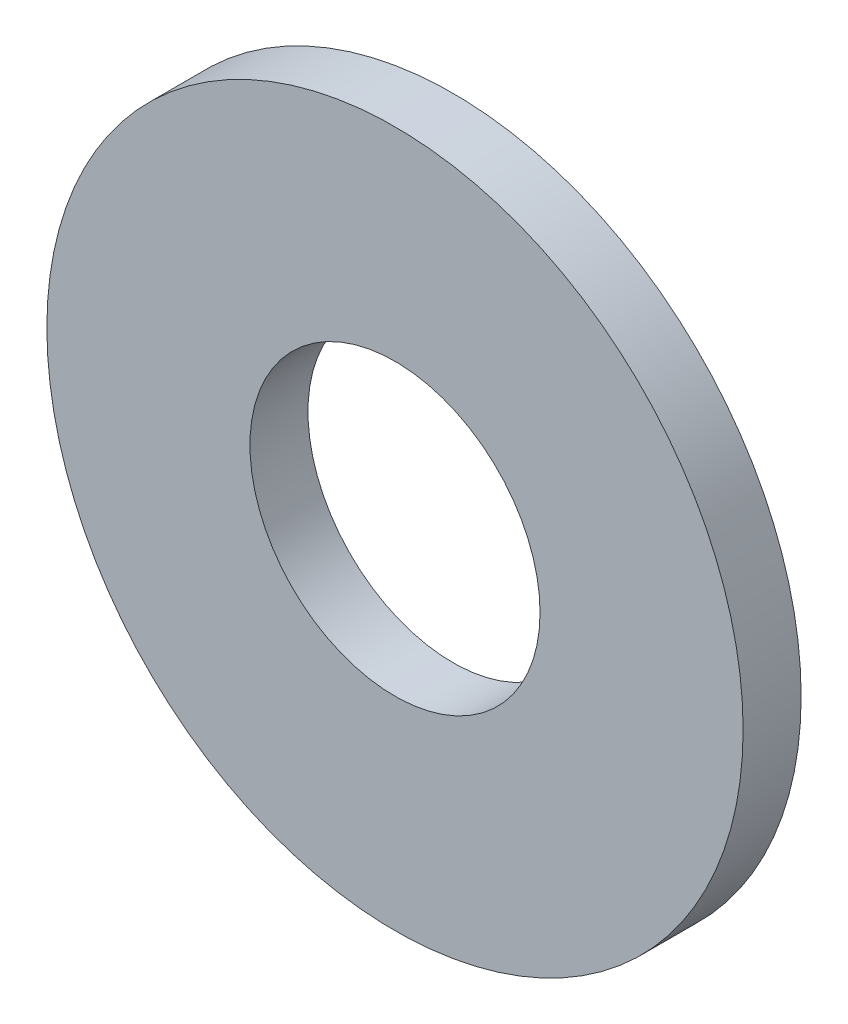
SolidWorks part; units mm, degrees
material "Plain Carbon Steel"
ref_plane "Front" through (0, 0, 0) normal (0, 0, 1) x (1, 0, 0)
ref_plane "Top" through (0, 0, 0) normal (0, 1, 0) x (1, 0, 0)
ref_plane "Right" through (0, 0, 0) normal (1, 0, 0) x (0, 0, -1)
sketch "Sketch1" plane through (0, 0, 0) normal (0, 0, 1) x (1, 0, 0)
  circle A0 centre (0, 0) radius 2.5
  circle A1 centre (0, 0) radius 6
  dimension "D1" = 12
  dimension "D2" = 5
extrude "Boss-Extrude1" add sketch "Sketch1" along normal blind 1
